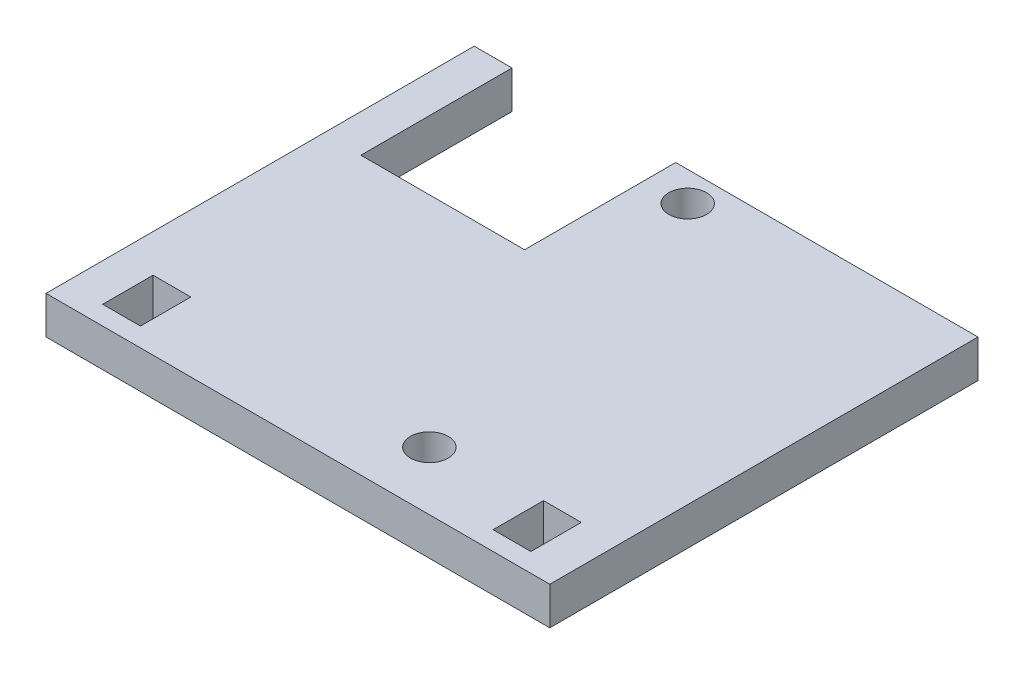
SolidWorks part; units mm, degrees
ref_plane "Front Plane" through (0, 0, 0) normal (0, 0, 1) x (1, 0, 0)
ref_plane "Top Plane" through (0, 0, 0) normal (0, 1, 0) x (1, 0, 0)
ref_plane "Right Plane" through (0, 0, 0) normal (1, 0, 0) x (0, 0, -1)
sketch "Sketch1" plane through (0, 0, 0) normal (0, 1, 0) x (1, 0, 0)
  line L0 (16, 34) -> (40, 34)
  line L1 (0, 0) -> (40, 0)
  line L2 (0, 0) -> (0, 34)
  line L3 (0, 34) -> (3, 34)
  line L4 (40, 0) -> (40, 34)
  line L5 (3, 1.5) -> (6, 1.5)
  line L6 (3, 1.5) -> (3, 5.5)
  line L7 (3, 5.5) -> (6, 5.5)
  line L8 (6, 1.5) -> (6, 5.5)
  line L9 (34, 5.5) -> (37, 5.5)
  line L10 (34, 5.5) -> (34, 1.5)
  line L11 (34, 1.5) -> (37, 1.5)
  line L12 (37, 5.5) -> (37, 1.5)
  line L14 (16.8, 33.84) -> (28.3, 33.84) construction
  line L15 (3, 34) -> (3, 22)
  line L16 (3, 22) -> (16, 22)
  line L17 (16, 34) -> (16, 22)
  line L18 (16.8, 33.84) -> (16.8, 1.84) construction
  line L19 (16.8, 1.84) -> (28.3, 1.84) construction
  line L20 (28.3, 33.84) -> (28.3, 1.84) construction
  circle A0 centre (19.3, 31.65) radius 1.5
  circle A1 centre (25.8, 4.64) radius 1.5
  dimension "D18" = 3
  dimension "D20" = 2.5
  dimension "3" = 3
  dimension "D1" = 40
  dimension "D2" = 34
  dimension "D3" = 3
  dimension "D4" = 3
  dimension "D5" = 4
  dimension "D6" = 1.5
  dimension "D7" = 3
  dimension "D8" = 1.5
  dimension "D9" = 4
  dimension "D10" = 3
  dimension "D11" = 0.16
  dimension "D12" = 24
  dimension "D13" = 13
  dimension "D14" = 12
  dimension "D15" = 11.7
  dimension "D16" = 11.5
  dimension "D17" = 32
  dimension "D19" = 2.5
  dimension "2.5" = 2.35
  dimension "D21" = 2.8
extrude "Boss-Extrude1" add sketch "Sketch1" along normal blind 3
